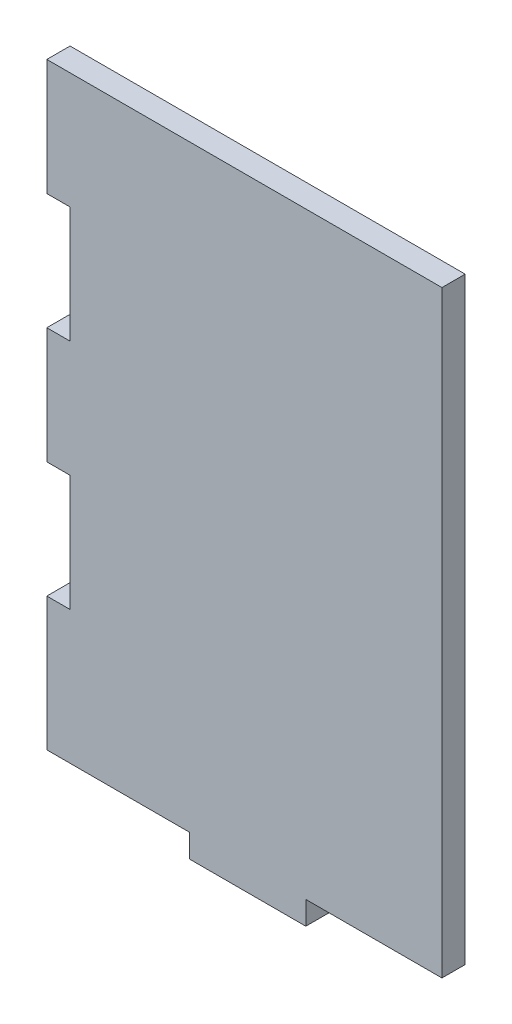
SolidWorks part; units mm, degrees
ref_plane "Front" through (0, 0, 0) normal (0, 0, 1) x (1, 0, 0)
ref_plane "Top" through (0, 0, 0) normal (0, 1, 0) x (1, 0, 0)
ref_plane "Right" through (0, 0, 0) normal (1, 0, 0) x (0, 0, -1)
sketch "Skizze1" plane through (0, 0, 0) normal (0, 0, 1) x (1, 0, 0)
  line L1 (17.0043, 25.7336) -> (-17.0043, 25.7336)
  line L2 (17.0043, 25.7336) -> (17.0043, -25.7336)
  line L3 (17.0043, -25.7336) -> (-17.0043, -25.7336)
  line L4 (-17.0043, 25.7336) -> (-17.0043, -25.7336)
  line L5 (17.0043, 25.7336) -> (-17.0043, -25.7336) construction
  line L6 (17.0043, -25.7336) -> (-17.0043, 25.7336) construction
  point P0 (0, 0)
extrude "Aufsatz-Linear austragen1" add sketch "Skizze1" along normal blind 2
sketch "Skizze6" plane through (0, -25.7336, 0) normal (0, -1, 0) x (1, 0, 0)
  line L0 (-17.0043, 0) -> (17.0043, 0) construction
  line L1 (5.2868, 0) -> (-4.7132, 0)
  line L2 (5.2868, 0) -> (5.2868, 2)
  line L3 (5.2868, 2) -> (-4.7132, 2)
  line L4 (-4.7132, 0) -> (-4.7132, 2)
  line L5 (-17.0043, 2) -> (17.0043, 2) construction
  dimension "D1" = 10
extrude "Aufsatz-Linear austragen2" add sketch "Skizze6" along normal blind 2
sketch "Skizze7" plane through (-17.0043, 0, 0) normal (-1, 0, 0) x (0, 0, 1)
  line L0 (0, 25.7336) -> (0, -25.7336) construction
  line L1 (0, 15.7336) -> (2, 15.7336)
  line L2 (0, 15.7336) -> (0, 5.7336)
  line L3 (0, 5.7336) -> (2, 5.7336)
  line L4 (2, 15.7336) -> (2, 5.7336)
  line L5 (2, 25.7336) -> (2, -25.7336) construction
  line L6 (2, 25.7336) -> (0, 25.7336) construction
  line L7 (2, -25.7336) -> (0, -25.7336) construction
  point P8 (1, 15.7336)
  point P11 (1, 5.7336)
  dimension "D1" = 10
  dimension "D2" = 2
  dimension "D3" = 10
  dimension "D4" = 31.4671
extrude "Schnitt-Linear austragen1" cut sketch "Skizze7" against normal blind 2
sketch "Skizze8" plane through (-17.0043, 0, 0) normal (-1, 0, 0) x (0, 0, 1)
  line L0 (0, 5.7336) -> (0, -25.7336) construction
  line L1 (0, -4.2664) -> (2, -4.2664)
  line L2 (0, -4.2664) -> (0, -14.2664)
  line L3 (0, -14.2664) -> (2, -14.2664)
  line L4 (2, -4.2664) -> (2, -14.2664)
  line L5 (2, 5.7336) -> (2, -25.7336) construction
  line L6 (0, 5.7336) -> (2, 5.7336) construction
  line L7 (2, -25.7336) -> (0, -25.7336) construction
  point P10 (1, -14.2664)
  dimension "D1" = 10
  dimension "D2" = 10
  dimension "D3" = 11.4671
extrude "Schnitt-Linear austragen2" cut sketch "Skizze8" against normal blind 2
